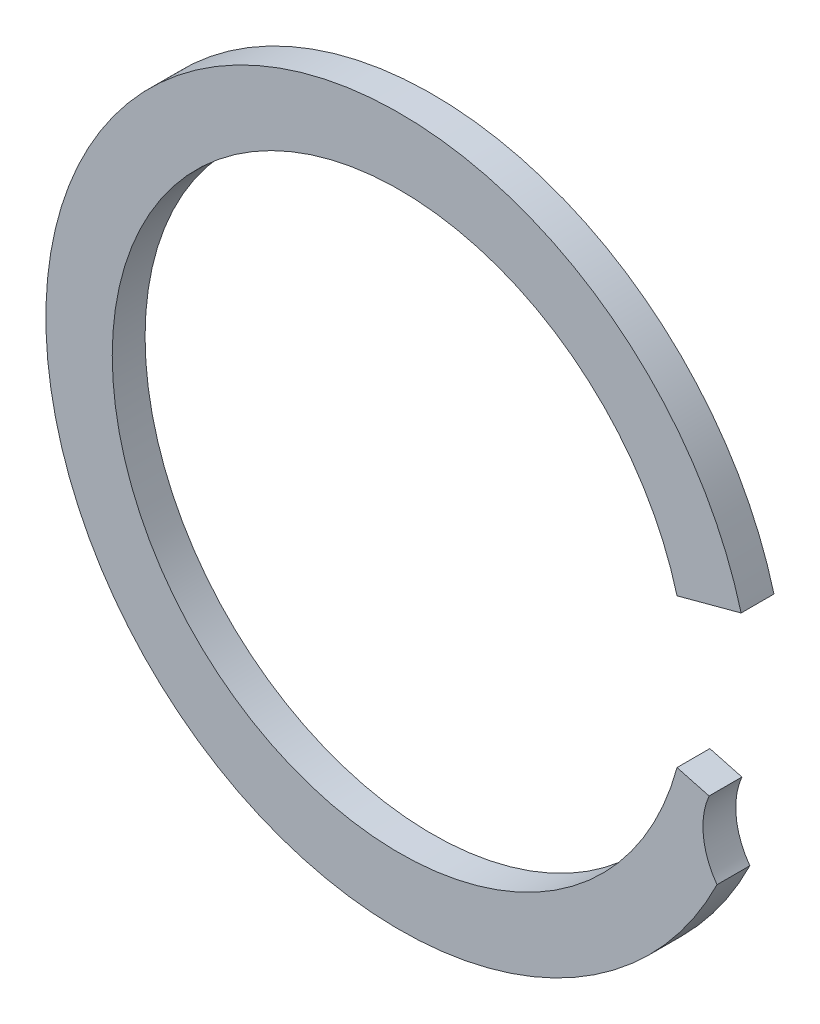
SolidWorks part; units mm, degrees
ref_plane "Front" through (0, 0, 0) normal (0, 0, 1) x (1, 0, 0)
ref_plane "Top" through (0, 0, 0) normal (0, 1, 0) x (1, 0, 0)
ref_plane "Right" through (0, 0, 0) normal (1, 0, 0) x (0, 0, -1)
sketch "Layout" plane through (0, 0, 0) normal (0, 0, 1) x (1, 0, 0)
  line L0 (-10.125, 0) -> (10.125, 0) construction
  line L1 (7.9447, -2.1288) -> (0, 0) construction
  line L2 (7.9447, 2.1288) -> (8.8624, 2.3747) construction
  line L3 (0, 0) -> (0, 2.5313) construction
  line L4 (0, 2.5313) -> (0, 5.0625) construction
  line L5 (0, 5.0625) -> (0, 7.5938) construction
  line L6 (0, 7.5938) -> (0, 10.125) construction
  line L7 (7.9447, 2.1288) -> (0, 0) construction
  line L9 (-10.125, 0) -> (-10.125, 0.94) construction
  line L10 (8.8624, 2.3747) -> (9.78, 2.6205) construction
  line L11 (7.9447, -2.1288) -> (8.8624, -2.3747) construction
  line L12 (8.8624, -2.3747) -> (9.78, -2.6205) construction
  line L13 (0, 7.5938) -> (15.234, 7.5938) construction
  circle A0 centre (0, 0) radius 8.225 construction
  circle A1 centre (0, 0) radius 10.125 construction
  circle A2 centre (7.2606, 0) radius 2.8644 construction
  circle A3 centre (15.234, 0) radius 7.5938 construction
  dimension "D1" = 15
sketch "Sketch2" plane through (0, 0, 0) normal (0, 0, 1) x (1, 0, 0)
  line L0 (-10.125, 0) -> (10.125, 0) construction
  line L1 (-10.125, 0) -> (10.125, 0) construction
  line L3 (7.9447, 2.1288) -> (8.8624, 2.3747) construction
  line L4 (8.8624, 2.3747) -> (9.78, 2.6205) construction
  line L5 (7.9447, -2.1288) -> (0, 0) construction
  line L6 (7.9447, -2.1288) -> (0, 0) construction
  line L8 (8.8624, -2.3747) -> (9.78, -2.6205) construction
  line L9 (7.9447, 2.1288) -> (8.8624, 2.3747)
  line L10 (8.8624, 2.3747) -> (9.78, 2.6205)
  line L11 (7.9447, -2.1288) -> (8.8624, -2.3747)
  circle A0 centre (0, 0) radius 10.125 construction
  circle A3 centre (0, 0) radius 8.225 construction
  circle A4 centre (15.234, 0) radius 7.5938 construction
  arc A5 (9.78, 2.6205) -> (9.0891, -4.4615) centre (0, 0) ccw
  arc A6 (7.9447, 2.1288) -> (7.9447, -2.1288) centre (0, 0) ccw
  arc A7 (8.8624, -2.3747) -> (9.0891, -4.4615) centre (10.799, -3.22) ccw
extrude "Boss-Extrude1" add sketch "Sketch2" along normal blind 0.94
sketch "Sketch3" plane through (0, 0, 0) normal (0, 0, 1) x (1, 0, 0)
  line L0 (0, 0) -> (9.78, 0) construction
  line L1 (5.816, -5.816) -> (7.1595, -7.1595) construction
  arc A0 (7.9447, 2.1288) -> (7.9447, -2.1288) centre (0, 0) ccw construction
  arc A1 (9.78, 2.6205) -> (9.0891, -4.4615) centre (0, 0) ccw construction
  dimension "D1" = 45
sketch "Sketch4" plane through (0, 0, 0) normal (0, 0, 1) x (1, 0, 0)
  circle A0 centre (0, 0) radius 10.125 construction
  arc A1 (9.78, 2.6205) -> (9.0891, -4.4615) centre (0, 0) ccw construction
equation "\"D1@Boss-Extrude1\"=\"thickness@Layout\""
